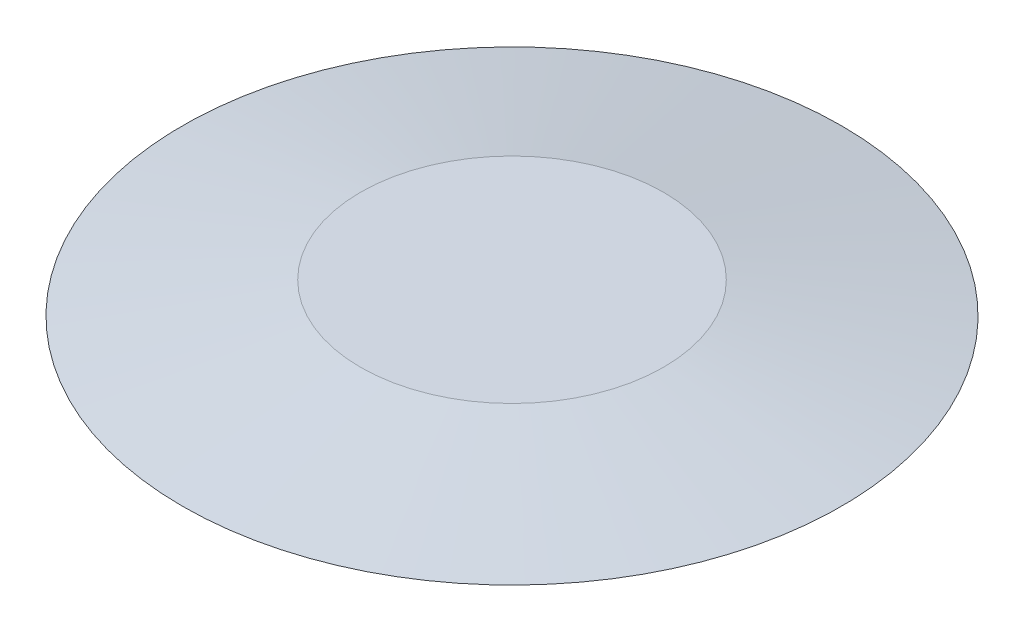
SolidWorks part; units mm, degrees
ref_plane "Alzado" through (0, 0, 0) normal (0, 0, 1) x (1, 0, 0)
ref_plane "Planta" through (0, 0, 0) normal (0, 1, 0) x (1, 0, 0)
ref_plane "Vista lateral" through (0, 0, 0) normal (1, 0, 0) x (0, 0, -1)
sketch "Croquis1" plane through (0, 0, 0) normal (0, 1, 0) x (1, 0, 0)
  circle A0 centre (0, 0) radius 26.67
  dimension "D1" = 53.34
extrude "Saliente-Extruir1" add sketch "Croquis1" along normal blind 2.54 draft 80
